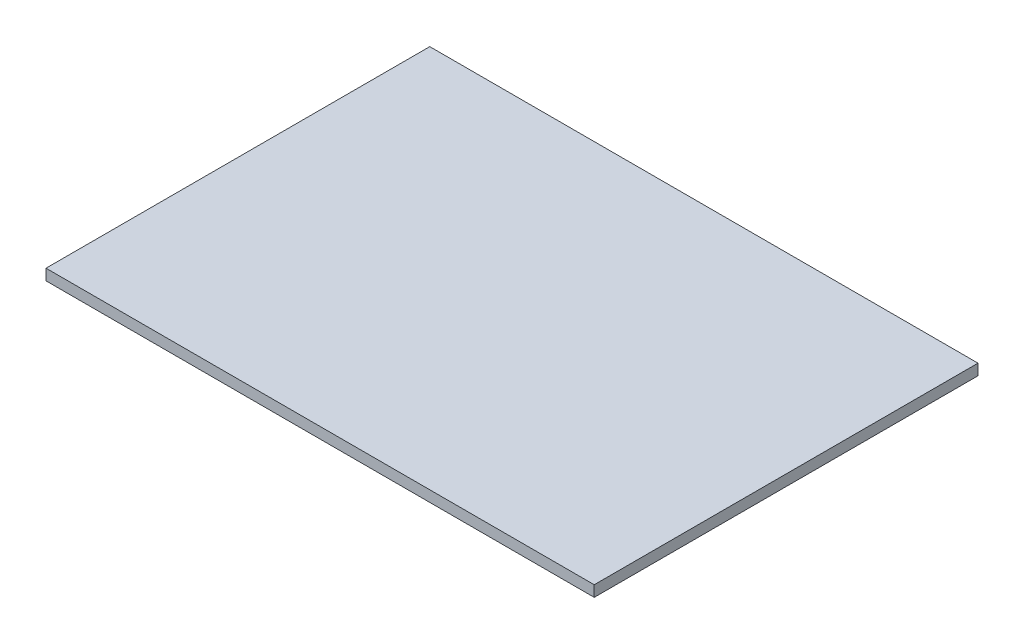
SolidWorks part; units mm, degrees
material "uhlíková ocel 7850"
ref_plane "Přední rovina" through (0, 0, 0) normal (0, 0, 1) x (1, 0, 0)
ref_plane "Horní rovina" through (0, 0, 0) normal (0, 1, 0) x (1, 0, 0)
ref_plane "Pravá rovina" through (0, 0, 0) normal (1, 0, 0) x (0, 0, -1)
sketch "Skica1" plane through (0, 0, 0) normal (0, 0, 1) x (1, 0, 0)
  line L1 (0, 0) -> (500, 0)
  line L2 (0, 0) -> (0, -10)
  line L3 (0, -10) -> (500, -10)
  line L4 (500, 0) -> (500, -10)
  dimension "D1" = 500
  dimension "D2" = 10
extrude "Přidat vysunutím1" add sketch "Skica1" along normal mid plane 350
